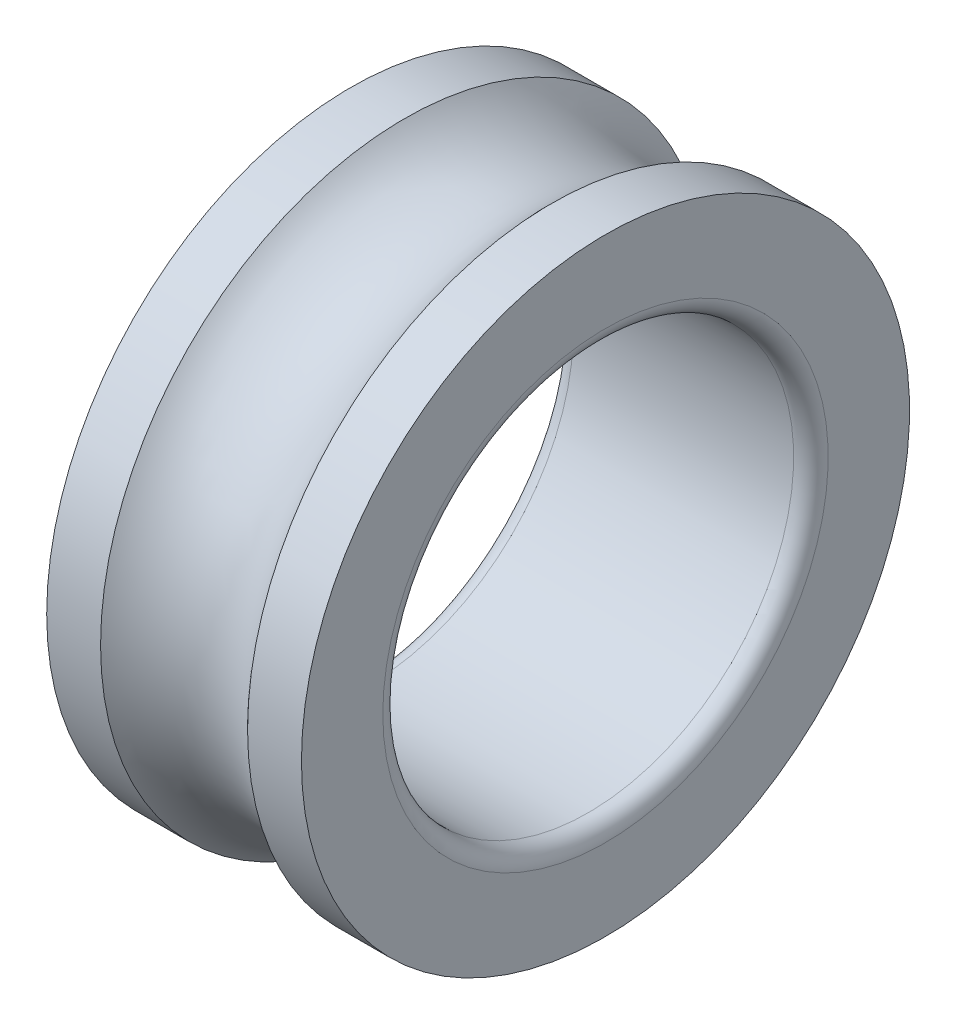
SolidWorks part; units mm, degrees
ref_plane "Front Plane" through (0, 0, 0) normal (0, 0, 1) x (1, 0, 0)
ref_plane "Top Plane" through (0, 0, 0) normal (0, 1, 0) x (1, 0, 0)
ref_plane "Right Plane" through (0, 0, 0) normal (1, 0, 0) x (0, 0, -1)
sketch "Sketch1" plane through (0, 0, 0) normal (0, 0, 1) x (1, 0, 0)
  line L0 (-44.3281, 0) -> (60.6346, 0) construction
  line L1 (8.9443, 37) -> (15.5, 37)
  line L2 (-15.5, 37) -> (-8.9443, 37)
  line L3 (-15.5, 37) -> (-15.5, 27.1)
  line L4 (-13.4, 25) -> (13.4, 25)
  line L5 (15.5, 37) -> (15.5, 27.1)
  line L6 (-15.5, 37) -> (15.5, 25) construction
  line L7 (-15.5, 25) -> (15.5, 37) construction
  line L8 (0, 25) -> (0, 0) construction
  arc A0 (8.9443, 37) -> (-8.9443, 37) centre (0, 45) cw
  arc A1 (13.4, 25) -> (15.5, 27.1) centre (13.4, 27.1) ccw
  arc A2 (-13.4, 25) -> (-15.5, 27.1) centre (-13.4, 27.1) cw
  point P3 (0, 31)
  dimension "D5" = 12
  dimension "D6" = 2.1
  dimension "D1" = 25
  dimension "D2" = 37
  dimension "D3" = 31
  dimension "D4" = 8
revolve "Revolve1" add sketch "Sketch1" angle 360 about L0
